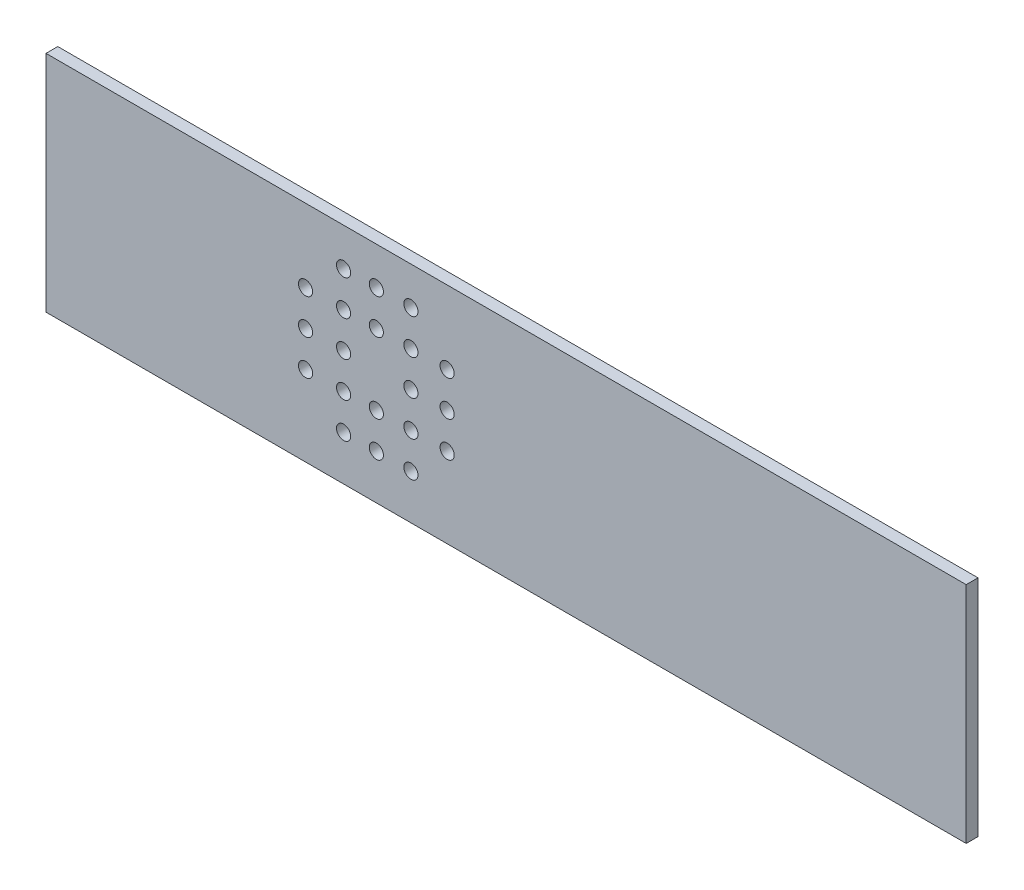
SolidWorks part; units mm, degrees
material "PVB"
ref_plane "Alzado" through (0, 0, 0) normal (0, 0, 1) x (1, 0, 0)
ref_plane "Planta" through (0, 0, 0) normal (0, 1, 0) x (1, 0, 0)
ref_plane "Vista lateral" through (0, 0, 0) normal (1, 0, 0) x (0, 0, -1)
sketch "Croquis1" plane through (0, 0, 0) normal (0, 0, 1) x (1, 0, 0)
  line L0 (92.1891, -37.2408) -> (152.1891, -37.2408) construction
  line L1 (-17.8109, 8.777) -> (372.1891, 8.777)
  line L2 (-17.8109, 8.777) -> (-17.8109, -86.223)
  line L3 (-17.8109, -86.223) -> (372.1891, -86.223)
  line L4 (372.1891, 8.777) -> (372.1891, -86.223)
  line L5 (122.1891, -37.2408) -> (122.1891, -7.2408) construction
  line L6 (122.1891, -37.2408) -> (122.1891, -67.2408) construction
  circle A0 centre (92.1891, -37.2408) radius 3
  circle A1 centre (152.1891, -37.2408) radius 3
  circle A2 centre (108.3068, -37.2408) radius 3
  circle A3 centre (122.1891, -7.2408) radius 3
  circle A4 centre (122.1891, -67.2408) radius 3
  circle A5 centre (122.1891, -52.2408) radius 3
  circle A6 centre (136.8446, -37.2408) radius 3
  circle A7 centre (122.1891, -22.2408) radius 3
  circle A8 centre (136.8446, -52.2408) radius 3
  circle A9 centre (108.3068, -52.2408) radius 3
  circle A10 centre (136.8446, -22.2408) radius 3
  circle A11 centre (108.3068, -22.2408) radius 3
  circle A12 centre (152.1891, -22.2408) radius 3
  circle A13 centre (136.8446, -7.2408) radius 3
  circle A14 centre (152.1891, -52.2408) radius 3
  circle A15 centre (136.8446, -67.2408) radius 3
  circle A16 centre (108.3068, -67.2408) radius 3
  circle A17 centre (92.1891, -52.2408) radius 3
  circle A18 centre (92.1891, -22.2408) radius 3
  circle A19 centre (108.3068, -7.2408) radius 3
  point P15 (0, 0)
  point P18 (122.1891, -52.2408)
  point P21 (136.8446, -37.2408)
  point P22 (108.3068, -37.2408)
  point P25 (122.1891, -22.2408)
  point P28 (136.8446, -52.2408)
  point P31 (108.3068, -52.2408)
  point P34 (136.8446, -22.2408)
  point P37 (108.3068, -22.2408)
  point P40 (152.1891, -22.2408)
  point P43 (136.8446, -7.2408)
  point P46 (152.1891, -52.2408)
  point P49 (136.8446, -67.2408)
  point P52 (108.3068, -67.2408)
  point P55 (92.1891, -52.2408)
  point P58 (0, 0)
  point P59 (92.1891, -22.2408)
  point P62 (108.3068, -7.2408)
  dimension "D3" = 110
  dimension "D4" = 170
  dimension "D1" = 390
  dimension "D2" = 95
extrude "Saliente-Extruir1" add sketch "Croquis1" along normal blind 5
